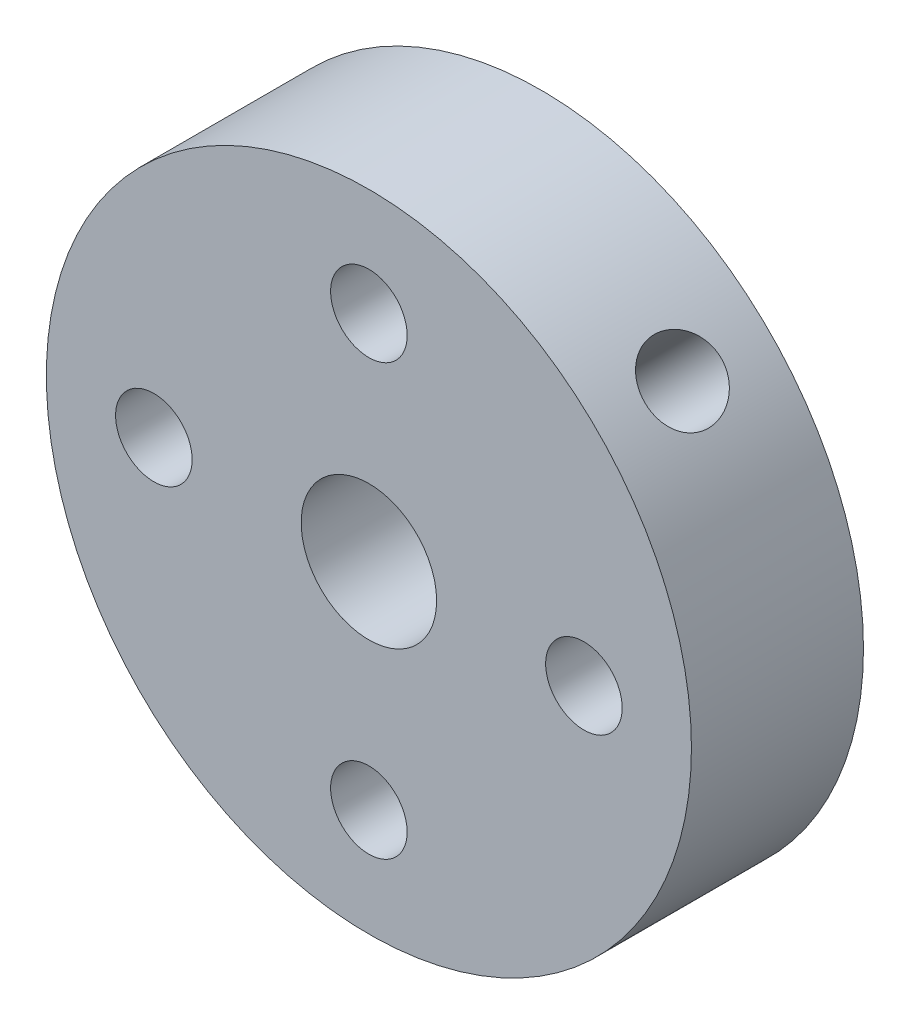
SolidWorks part; units mm, degrees
material "1060 Alloy"
ref_plane "Front Plane" through (0, 0, 0) normal (0, 0, 1) x (1, 0, 0)
ref_plane "Top Plane" through (0, 0, 0) normal (0, 1, 0) x (1, 0, 0)
ref_plane "Right Plane" through (0, 0, 0) normal (1, 0, 0) x (0, 0, -1)
sketch "Sketch1" plane through (0, 0, 0) normal (0, 0, 1) x (1, 0, 0)
  line L0 (0, 0) -> (6.7352, 6.7352) construction
  line L1 (6.7352, 6.7352) -> (6.35, 0) construction
  line L2 (6.35, 0) -> (6.7352, 6.7352) construction
  line L3 (6.7352, 6.7352) -> (0, 6.35) construction
  circle A0 centre (0, 0) radius 9.525
  circle A1 centre (0, 0) radius 2
  circle A2 centre (-6.35, 0) radius 1.1303
  circle A3 centre (0, 6.35) radius 1.1303
  circle A4 centre (6.35, 0) radius 1.1303
  circle A5 centre (0, -6.35) radius 1.1303
  dimension "D1" = 19.05
  dimension "D2" = 4
  dimension "D4" = 2.2606
  dimension "D3" = 6.35
  dimension "D5" = 4
extrude "Boss-Extrude1" add sketch "Sketch1" along normal blind 5.08
ref_plane "Plane1" through (6.7352, 6.7352, 0) normal (0.7071, 0.7071, 0) x (-0.7071, 0.7071, 0)
sketch "Sketch2" plane through (6.7352, 6.7352, 0) normal (0.7071, 0.7071, 0) x (-0.7071, 0.7071, 0)
  circle A0 centre (0, 2.54) radius 1.1303
  dimension "D1" = 2.2606
  dimension "D2" = 2.54
extrude "Cut-Extrude1" cut sketch "Sketch2" against normal blind 10.16
ref_plane "Plane2" through (2.3758, -2.3758, 0) normal (0.7071, -0.7071, 0) x (-0.7071, -0.7071, 0)
